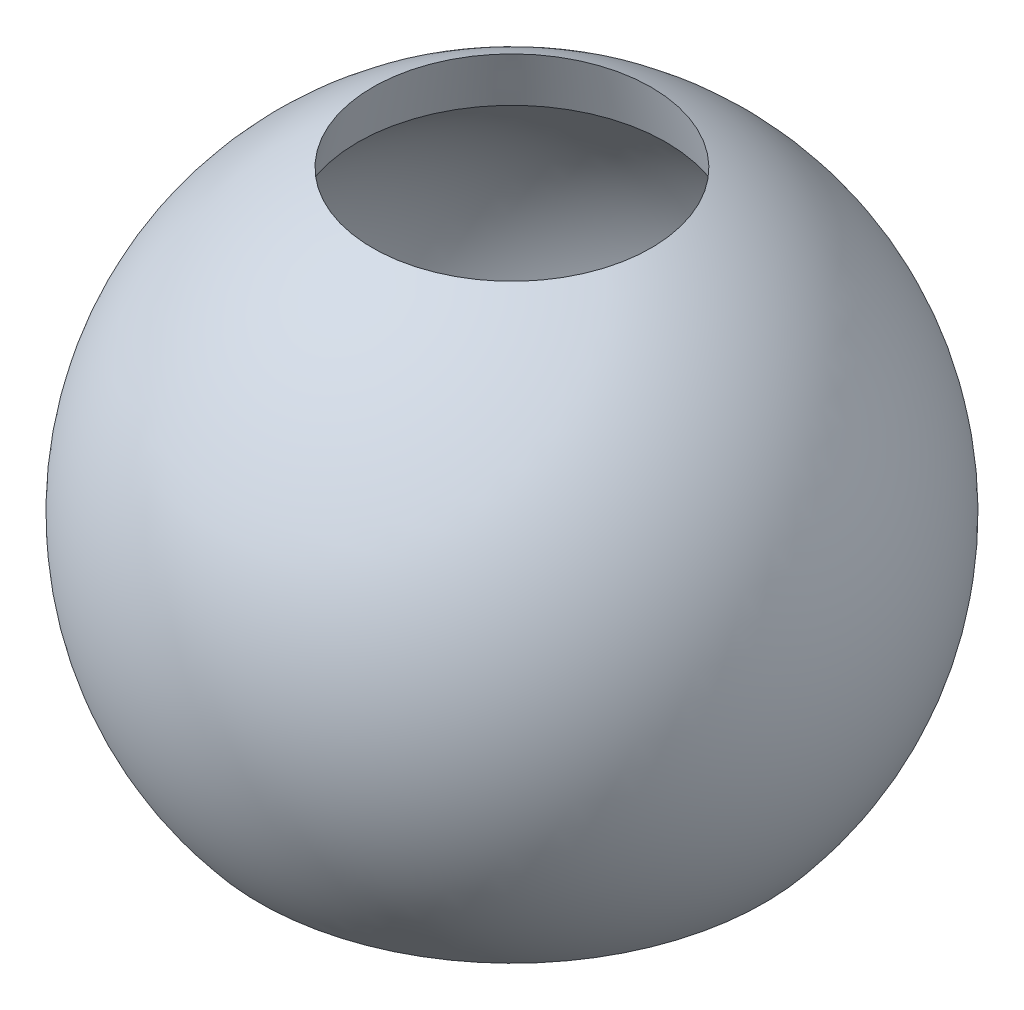
SolidWorks part; units mm, degrees
ref_plane "Front Plane" through (0, 0, 0) normal (0, 0, 1) x (1, 0, 0)
ref_plane "Top Plane" through (0, 0, 0) normal (0, 1, 0) x (1, 0, 0)
ref_plane "Right Plane" through (0, 0, 0) normal (1, 0, 0) x (0, 0, -1)
sketch "Sketch1" plane through (0, 0, 0) normal (1, 0, 0) x (0, 0, -1)
  line L0 (-5.6073, 8.8757) -> (-5.0714, 10.8757)
  line L1 (-7.122, -7.7135) -> (-9.1925, -7.7135)
  line L2 (0, 0) -> (0, 13.0758) construction
  line L3 (0, 0) -> (-46.4165, 0) construction
  line L4 (-5.0714, 10.8757) -> (0, 0) construction
  line L5 (0, 0) -> (-9.1925, -7.7135) construction
  arc A0 (-5.0714, 10.8757) -> (-9.1925, -7.7135) centre (0, 0) ccw
  arc A1 (-5.6073, 8.8757) -> (-7.122, -7.7135) centre (0, 0) ccw
revolve "Revolve1" add sketch "Sketch1" angle 360 about L2
equation "\"thick\"= 2mm"
equation "\"D1@Sketch1\"=\"thick\""
